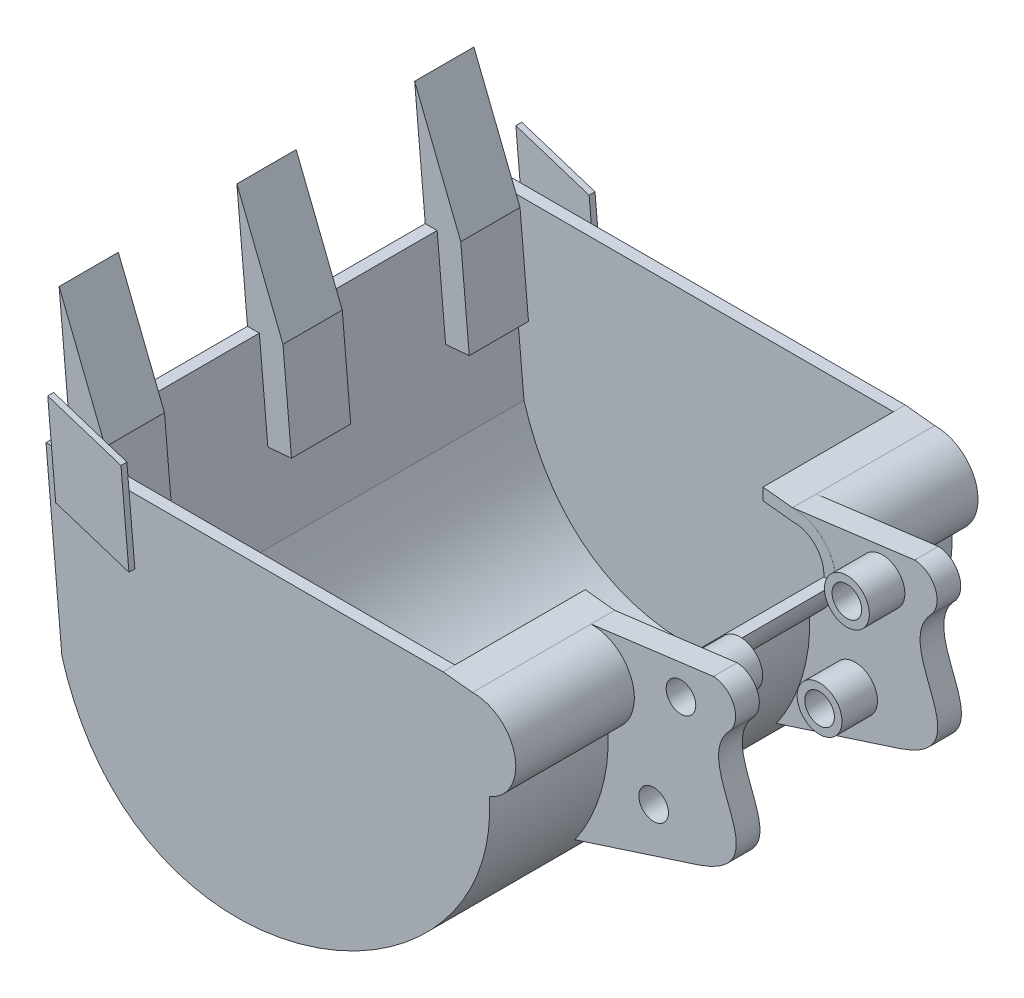
SolidWorks part; units mm, degrees
ref_plane "Front Plane" through (0, 0, 0) normal (0, 0, 1) x (1, 0, 0)
ref_plane "Top Plane" through (0, 0, 0) normal (0, 1, 0) x (1, 0, 0)
ref_plane "Right Plane" through (0, 0, 0) normal (1, 0, 0) x (0, 0, -1)
sketch "Sketch1" plane through (0, 0, 0) normal (0, 0, 1) x (1, 0, 0)
  line L0 (130, 0) -> (-130, 0)
  line L9 (130, 0) -> (130, -80) construction
  line L12 (130, 0) -> (154.8586, -2.6547)
  line L14 (-191.5919, -149.3995) -> (130, -80) construction
  line L17 (-130, 0) -> (-205, 0)
  line L18 (-205, 0) -> (-191.5919, -149.3995)
  line L19 (130, -80) -> (169.0999, -71.5622) construction
  line L20 (-30.7959, -114.6998) -> (0.8457, -261.3245) construction
  arc A3 (154.8586, -2.6547) -> (169.0999, -71.5622) centre (155.6323, -38.4202) cw
  spline S0 degree 3 poles (-191.5919, -149.3995) (-126.4253, -370.0907) (179.8541, -241.3594) (169.0999, -71.5622) knots 0 0 0 0 1 1 1 1
  point P4 (0, 0)
  dimension "D6" = 260
  dimension "D7" = 25
extrude "Basic_geometry" add sketch "Sketch1" along normal mid plane 390
shell "Remove_material" thickness 10
sketch "Sketch2" plane through (0, 0, 0) normal (0, 1, 0) x (1, 0, 0)
  line L0 (35.8281, -185) -> (130, -185)
  line L3 (130, -195) -> (130, 195) construction
  line L5 (159.3763, -185) -> (-181.7215, -185) construction
  line L6 (130, -185) -> (130, 185)
  line L8 (-181.7215, 185) -> (159.3763, 185) construction
  line L9 (130, 185) -> (35.8281, 185)
  line L10 (35.8281, 185) -> (35.8281, -185)
sketch "Sketch7" plane through (0, 0, -185) normal (0, 0, 1) x (1, 0, 0)
  line L9 (-205, 0) -> (-213.9387, 99.5997)
  line L10 (-205, 0) -> (-194.9598, 0)
  line L11 (-194.9598, 0) -> (-187.8088, -79.6798)
  line L12 (-194.9598, 0) -> (-181.7215, -147.5077) construction
  line L13 (-187.8088, -79.6798) -> (-167.8889, -77.892)
  line L14 (-167.8889, -77.892) -> (-175.0399, 1.7877)
  line L15 (-213.9387, 99.5997) -> (-175.0399, 1.7877)
extrude "Teeth" add sketch "Sketch7" along normal blind 50 from offset 10
extrude "Remove_material2" cut sketch "Sketch2" against normal blind 50
pattern_linear "Teeth_pattern" count 3 spacing 150 along (0, 0, 1) of "Teeth"
sketch "Sketch8" plane through (0, 0, 195) normal (0, 0, 1) x (1, 0, 0)
  line L0 (-194.9598, 0) -> (-198.5353, 39.8399)
  line L1 (-194.9598, 0) -> (-134.9598, 0) construction
  line L2 (130, 0) -> (-205, 0) construction
  line L5 (-194.9598, 0) -> (-191.8312, -34.8599)
  line L6 (-134.9598, 0) -> (-136.7476, 19.9199)
  line L7 (-198.5353, 39.8399) -> (-136.7476, 19.9199)
  line L8 (-134.9598, 0) -> (-130.0435, -54.7798)
  line L9 (-191.8312, -34.8599) -> (-130.0435, -54.7798)
extrude "Side_plate" add sketch "Sketch8" along normal blind 5
mirror "Side_plate_mirror" about plane through (0, 0, 0) normal (0, 0, 1) of "Side_plate"
sketch "Sketch9" plane through (0, 0, 0) normal (0, 0, 1) x (1, 0, 0)
  line L0 (141.2967, -167.0571) -> (245.9674, -133.2334)
  line L1 (154.8586, -2.6547) -> (258.0999, 10.6957)
  arc A2 (154.8586, -2.6547) -> (169.0999, -71.5622) centre (155.6323, -38.4202) cw
  arc A3 (169.0999, -71.5622) -> (141.2967, -167.0571) centre (14.1795, -78.2523) cw
  arc A4 (258.0999, 10.6957) -> (272.5947, -21.4623) centre (256.9746, -9.1572) cw
  spline S0 degree 3 poles (-191.5919, -149.3995) (-126.4253, -370.0907) (179.8541, -241.3594) (169.0999, -71.5622) knots 0 0 0 0 1 1 1 1 construction
  spline S1 degree 3 poles (272.5947, -21.4623) (235.1132, -59.3334) (319.8726, -107.999) (245.9674, -133.2334) knots 0 0 0 0 1 1 1 1
extrude "Boss-Extrude6" add sketch "Sketch9" along direction (0, 0, 1) on the side of the normal blind 20 from offset 75 separate body
pattern_linear "LPattern4" count 2 spacing 170 along (0, 0, 1) of "Boss-Extrude6"
sketch "Sketch10" plane through (0, 0, 95) normal (0, 0, 1) x (1, 0, 0)
  line L0 (207.704, -108.0476) -> (230.3763, -108.0476) construction
  line L1 (258.0999, 10.6957) -> (154.8586, -2.6547) construction
  line L2 (-213.9387, 99.5997) -> (230.7624, -18.0476) construction
  line L3 (-213.9387, 99.5997) -> (207.704, -108.0476) construction
  circle A1 centre (230.7624, -18.0476) radius 12.5
  circle A2 centre (207.704, -108.0476) radius 12.5
  dimension "D1" = 25
  dimension "D2" = 25
  dimension "D3" = 90
  dimension "D4" = 25
  dimension "D5" = 460
  dimension "D6" = 470
extrude "Cut-Extrude4" cut sketch "Sketch10" against normal through all
sketch "Sketch11" plane through (0, 0, 75) normal (0, 0, -1) x (-1, 0, 0)
  circle A1 centre (-230.7624, -18.0476) radius 18.9115
  circle A2 centre (-230.7624, -18.0476) radius 12.5
  circle A3 centre (-207.704, -108.0476) radius 18.9115
  circle A4 centre (-207.704, -108.0476) radius 12.5
extrude "Boss-Extrude7" add sketch "Sketch11" along normal blind 30
pattern_linear "LPattern7" count 2 spacing 120 along (0, 0, -1) of "Boss-Extrude7"
sketch "Sketch13" plane through (130, 0, 0) normal (-1, 0, 0) x (0, 0, 1)
  line L0 (-25, 0) -> (-125, 0) construction
  line L1 (-75, 0) -> (75, 0)
  line L2 (-75, 0) -> (-75, -40)
  line L3 (-75, -40) -> (75, -40)
  line L4 (75, 0) -> (75, -40)
extrude "Cut-Extrude5" cut sketch "Sketch13" against normal blind 70
ref_plane "Mid plane" through (0, 0, 0) normal (0, 0, -1) x (-1, 0, 0)
ref_point "Point1"
sketch "Sketch14" plane through (0, 0, 95) normal (0, 0, 1) x (1, 0, 0)
  line L0 (230.7624, -18.0476) -> (243.2624, -18.0476)
  line L1 (230.7624, -18.0476) -> (230.7624, -5.5476)
  circle A0 centre (230.7624, -18.0476) radius 12.5 construction
ref_plane "Angle plane" through (230.7624, 0, 0) normal (-1, 0, 0) x (0, 1, 0)
